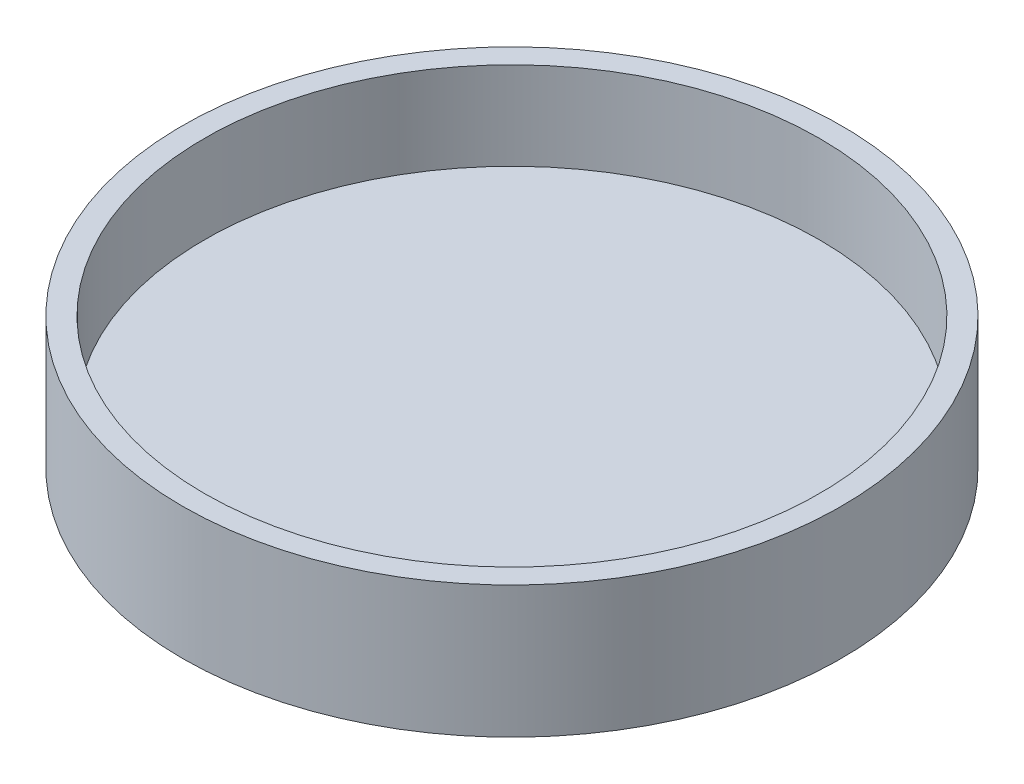
SolidWorks part; units mm, degrees
ref_plane "Front Plane" through (0, 0, 0) normal (0, 0, 1) x (1, 0, 0)
ref_plane "Top Plane" through (0, 0, 0) normal (0, 1, 0) x (1, 0, 0)
ref_plane "Right Plane" through (0, 0, 0) normal (1, 0, 0) x (0, 0, -1)
sketch "Sketch1" plane through (0, 0, 0) normal (0, 1, 0) x (1, 0, 0)
  circle A0 centre (0, 0) radius 190.5
  dimension "D1" = 381
extrude "Boss-Extrude1" add sketch "Sketch1" along normal blind 25.4
sketch "Sketch2" plane through (0, 25.4, 0) normal (0, 1, 0) x (1, 0, 0)
  circle A0 centre (0, 0) radius 177.8
  circle A1 centre (0, 0) radius 190.5
  dimension "D1" = 355.6
  dimension "D2" = 381
extrude "Boss-Extrude2" add sketch "Sketch2" along normal blind 50.8 contours A0
sketch "Sketch3" plane through (0, 25.4, 0) normal (0, 1, 0) x (1, 0, 0)
  line L1 (-95.25, 101.6) -> (95.25, 101.6)
  line L2 (-95.25, 101.6) -> (-95.25, -101.6)
  line L3 (-95.25, -101.6) -> (95.25, -101.6)
  line L4 (95.25, 101.6) -> (95.25, -101.6)
  line L5 (-95.25, 101.6) -> (95.25, -101.6) construction
  line L6 (-95.25, -101.6) -> (95.25, 101.6) construction
  point P0 (0, 0)
  dimension "D1" = 190.5
  dimension "D2" = 203.2
